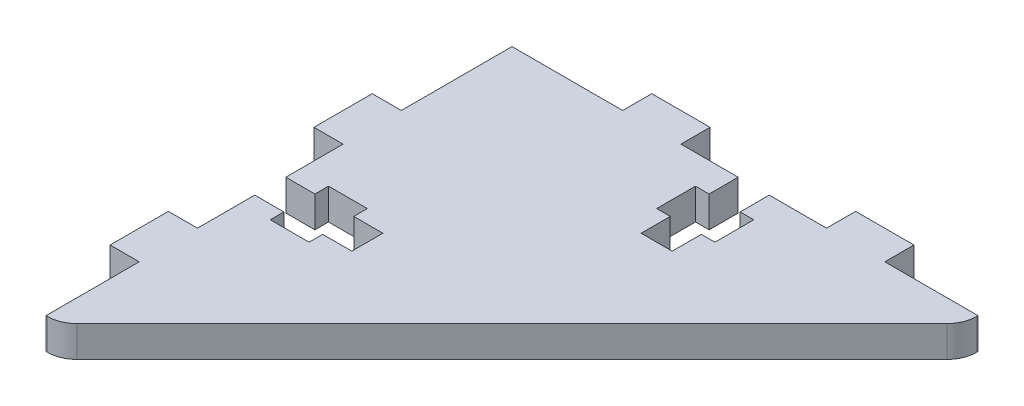
SolidWorks part; units mm, degrees
ref_plane "Alzado" through (0, 0, 0) normal (0, 0, 1) x (1, 0, 0)
ref_plane "Planta" through (0, 0, 0) normal (0, 1, 0) x (1, 0, 0)
ref_plane "Vista lateral" through (0, 0, 0) normal (1, 0, 0) x (0, 0, -1)
sketch "Croquis1" plane through (0, 0, 0) normal (0, 1, 0) x (1, 0, 0)
  line L0 (7, 21.5) -> (7, 20.1)
  line L1 (0, 0) -> (0.1716, 0)
  line L2 (0, 0) -> (0, 9.6)
  line L3 (0, 48) -> (11.4, 48)
  line L4 (48, 47.8284) -> (48, 48)
  line L6 (11.4, 48) -> (11.4, 51)
  line L7 (11.4, 51) -> (17.4, 51)
  line L8 (17.4, 48) -> (17.4, 51)
  line L10 (32.4, 48) -> (32.4, 51)
  line L11 (32.4, 51) -> (38.4, 51)
  line L12 (38.4, 48) -> (38.4, 51)
  line L14 (23.3, 48) -> (23.3, 45)
  line L15 (23.3, 38) -> (26.5, 38)
  line L16 (26.5, 48) -> (26.5, 45)
  line L17 (0, 36.6) -> (-3, 36.6)
  line L19 (0, 30.6) -> (-3, 30.6)
  line L20 (-3, 36.6) -> (-3, 30.6)
  line L21 (0, 15.6) -> (-3, 15.6)
  line L23 (0, 9.6) -> (-3, 9.6)
  line L24 (-3, 15.6) -> (-3, 9.6)
  line L25 (0, 24.7) -> (3, 24.7)
  line L27 (0, 21.5) -> (3, 21.5)
  line L28 (10, 24.7) -> (10, 21.5)
  line L29 (3, 26.1) -> (7, 26.1)
  line L30 (3, 26.1) -> (3, 24.7)
  line L31 (3, 20.1) -> (7, 20.1)
  line L32 (7, 26.1) -> (7, 24.7)
  line L33 (7, 24.7) -> (10, 24.7)
  line L34 (3, 21.5) -> (3, 20.1)
  line L35 (7, 21.5) -> (10, 21.5)
  line L36 (0, 36.6) -> (0, 48)
  line L37 (0, 15.6) -> (0, 30.6)
  line L38 (26.5, 41) -> (26.5, 38)
  line L39 (21.9, 45) -> (23.3, 45)
  line L40 (21.9, 45) -> (21.9, 41)
  line L41 (21.9, 41) -> (23.3, 41)
  line L42 (27.9, 45) -> (27.9, 41)
  line L43 (26.5, 45) -> (27.9, 45)
  line L44 (23.3, 41) -> (23.3, 38)
  line L45 (26.5, 41) -> (27.9, 41)
  line L46 (17.4, 48) -> (32.4, 48)
  line L47 (38.4, 48) -> (48, 48)
  line L48 (0, 0) -> (48, 48) construction
  line L49 (47.1213, 45.7071) -> (2.2929, 0.8787)
  arc A1 (47.1213, 45.7071) -> (48, 47.8284) centre (45, 47.8284) ccw
  arc A2 (2.2929, 0.8787) -> (0.1716, 0) centre (0.1716, 3) cw
  dimension "D30" = 3
  dimension "D31" = 3
  dimension "D1" = 48
  dimension "D2" = 48
  dimension "D3" = 6
  dimension "D4" = 3
  dimension "D5" = 3
  dimension "D6" = 6
  dimension "D7" = 15
  dimension "D8" = 10
  dimension "D9" = 3.2
  dimension "D10" = 5.9
  dimension "D11" = 11.4
  dimension "D12" = 3
  dimension "D13" = 3
  dimension "D14" = 6
  dimension "D15" = 6
  dimension "D16" = 15
  dimension "D17" = 11.4
  dimension "D18" = 3.2
  dimension "D19" = 10
  dimension "D20" = 5.9
  dimension "D21" = 4
  dimension "D22" = 6
  dimension "D23" = 3
  dimension "D24" = 1.4
  dimension "D25" = 4
  dimension "D26" = 6
  dimension "D27" = 3
  dimension "D28" = 1.4
  dimension "D29" = 1
extrude "Saliente-Extruir2" add sketch "Croquis1" along normal blind 3.2 contours L2 L48 L47 L12 L11 L10 L46 L16 L43 L42 L45 L38 L15 L44 L41 L40 L39 L14 L8 L7 L6 L3 L36 L17 L20 L19 L37 L25 L30 L29 L32 L33 L28 L35 L0 L31 L34 L27 L21 L24 L23 | L48 L1 A2 L49 A1 L4
